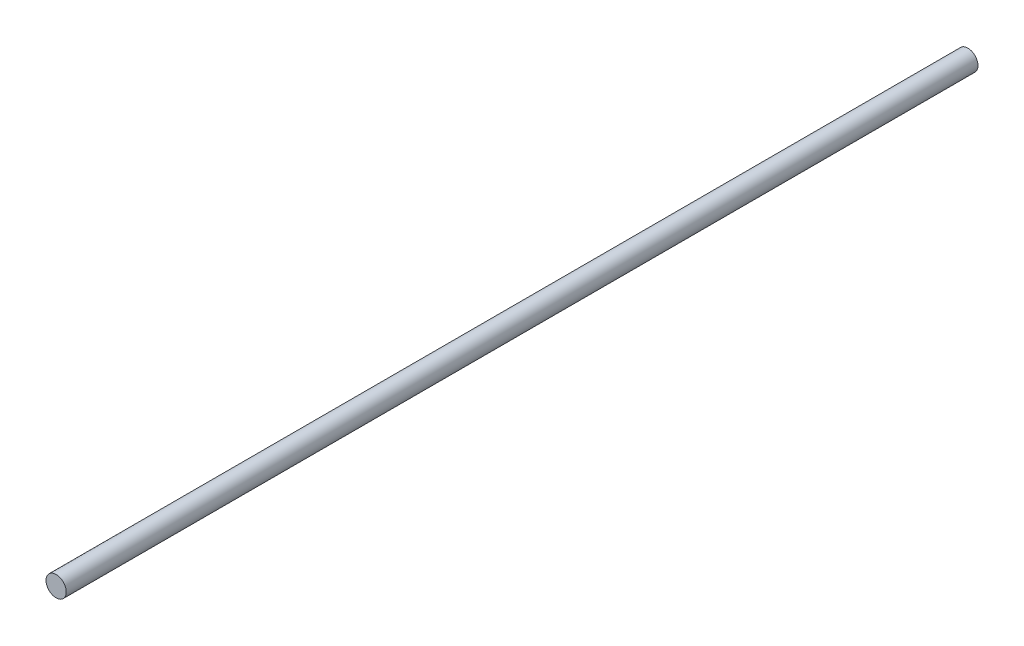
SolidWorks part; units mm, degrees
ref_plane "Plan de face" through (0, 0, 0) normal (0, 0, 1) x (1, 0, 0)
ref_plane "Plan de dessus" through (0, 0, 0) normal (0, 1, 0) x (1, 0, 0)
ref_plane "Plan de droite" through (0, 0, 0) normal (1, 0, 0) x (0, 0, -1)
sketch "Esquisse1" plane through (0, 0, 0) normal (0, 0, 1) x (1, 0, 0)
  circle A0 centre (0, 0) radius 4
  dimension "D1" = 8
extrude "Boss.-Extru.1" add sketch "Esquisse1" along normal blind 360
